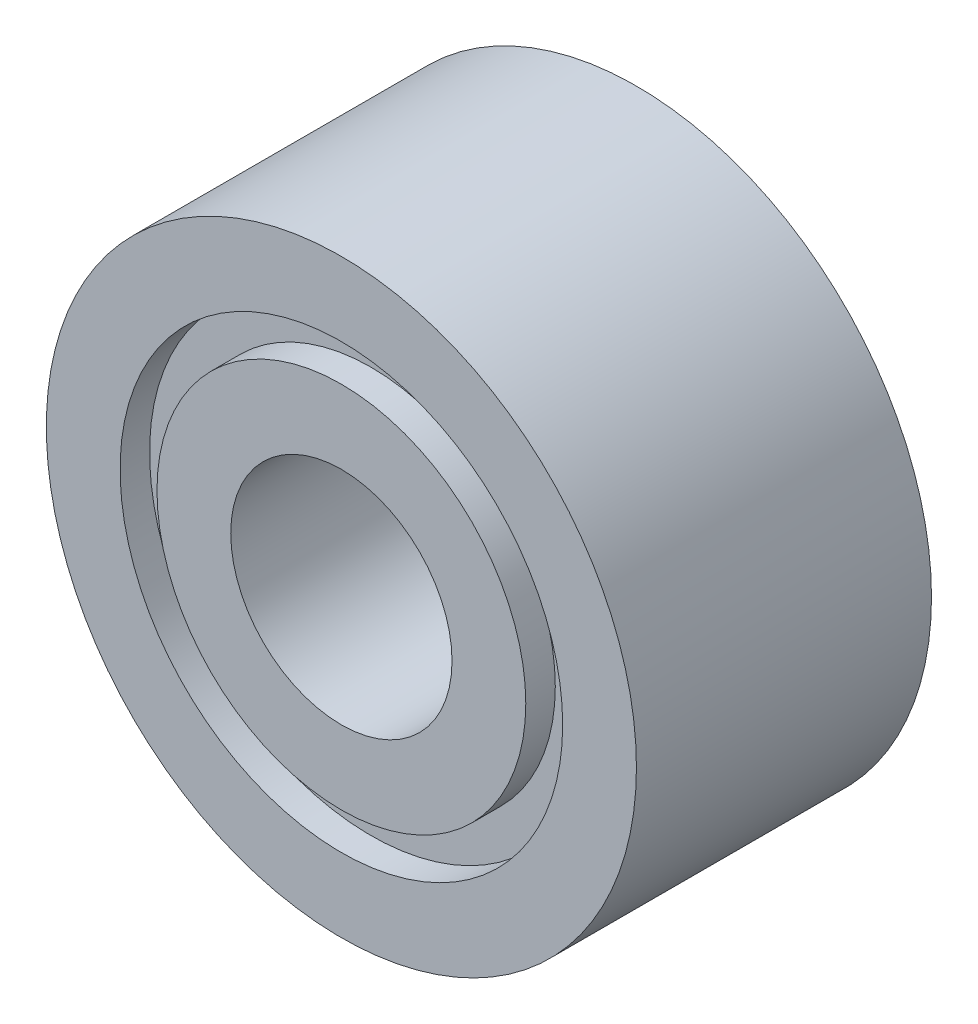
SolidWorks part; units mm, degrees
ref_plane "Front Plane" through (0, 0, 0) normal (0, 0, 1) x (1, 0, 0)
ref_plane "Top Plane" through (0, 0, 0) normal (0, 1, 0) x (1, 0, 0)
ref_plane "Right Plane" through (0, 0, 0) normal (1, 0, 0) x (0, 0, -1)
sketch "Sketch2" plane through (0, 0, 0) normal (1, 0, 0) x (0, 0, -1)
  line L0 (0, 0) -> (4.251, 0) construction
  line L1 (1.1092, 2) -> (3.1092, 2)
  line L2 (3.1092, 2) -> (3.1092, 1.5)
  line L3 (3.1092, 1.5) -> (2.9092, 1.5)
  line L4 (2.9092, 1.5) -> (2.9092, 1.25)
  line L5 (2.9092, 1.25) -> (3.1092, 1.25)
  line L6 (3.1092, 1.25) -> (3.1092, 0.75)
  line L7 (3.1092, 0.75) -> (1.1092, 0.75)
  line L8 (1.1092, 0.75) -> (1.1092, 1.25)
  line L9 (1.1092, 1.25) -> (1.3092, 1.25)
  line L10 (1.3092, 1.25) -> (1.3092, 1.5)
  line L11 (1.3092, 1.5) -> (1.1092, 1.5)
  line L12 (1.1092, 1.5) -> (1.1092, 2)
  point P14 (2.1092, 2)
  point P16 (2.1092, 0.75)
  dimension "D1" = 2
  dimension "D2" = 1.5
  dimension "D3" = 4
  dimension "D4" = 0.5
  dimension "D5" = 0.2
  dimension "D6" = 0.5
revolve "Revolve1" add sketch "Sketch2" angle 360 about L0
